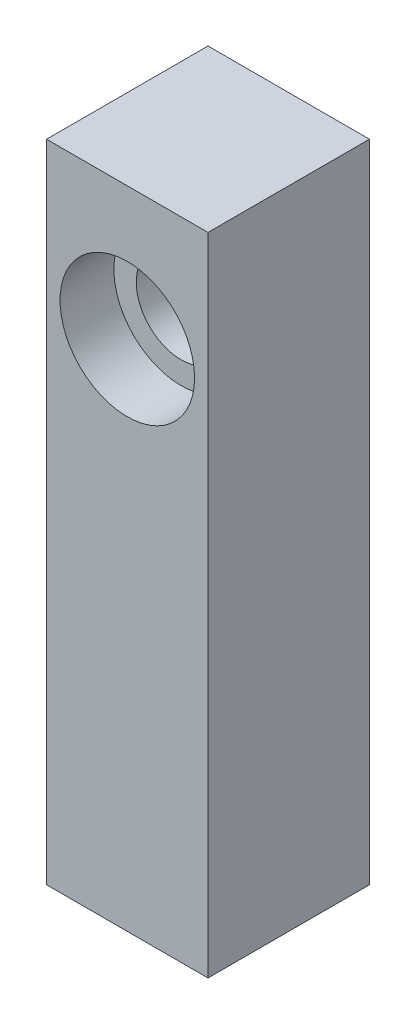
SolidWorks part; units mm, degrees
ref_plane "Front Plane" through (0, 0, 0) normal (0, 0, 1) x (1, 0, 0)
ref_plane "Top Plane" through (0, 0, 0) normal (0, 1, 0) x (1, 0, 0)
ref_plane "Right Plane" through (0, 0, 0) normal (1, 0, 0) x (0, 0, -1)
sketch "Sketch1" plane through (0, 0, 0) normal (0, 1, 0) x (1, 0, 0)
  line L1 (-42.9588, -4.732) -> (-24.9588, -4.732)
  line L2 (-42.9588, -4.732) -> (-42.9588, 13.268)
  line L3 (-42.9588, 13.268) -> (-24.9588, 13.268)
  line L4 (-24.9588, -4.732) -> (-24.9588, 13.268)
  dimension "D1" = 18
  dimension "D2" = 18
extrude "Boss-Extrude1" add sketch "Sketch1" along normal blind 72
sketch "Sketch2" plane through (0, 0, 4.732) normal (0, 0, 1) x (1, 0, 0)
  line L0 (-42.9588, 0) -> (-24.9588, 0) construction
  line L1 (-24.9588, 72) -> (-24.9588, 0) construction
  circle A0 centre (-33.9588, 57.2) radius 5
  dimension "D1" = 57.2
  dimension "D2" = 9
  dimension "D3" = 10
extrude "Cut-Extrude1" cut sketch "Sketch2" against normal through all
sketch "Sketch3" plane through (0, 0, 0) normal (0, -1, 0) x (1, 0, 0)
  line L0 (-24.9588, 4.732) -> (-24.9588, -13.268) construction
  line L1 (-24.9588, -13.268) -> (-42.9588, -13.268) construction
  circle A0 centre (-33.9588, -4.268) radius 3
  dimension "D1" = 6
  dimension "D2" = 9
  dimension "D3" = 9
hole_wizard "M6x1.0 Tapped Hole1" positions "Sketch4" profile "Sketch5" tap size "M6x1.0" standard "ANSI Metric"
sketch "Sketch4" plane through (0, 0, 0) normal (0, -1, 0) x (-1, 0, 0)
  point P0 (33.9588, 4.268)
sketch "Sketch5" plane through (-33.9588, 0, -4.268) normal (1, 0, 0) x (0, 0, -1)
  line L0 (0, 0) -> (0, 30.5022)
  line L1 (0, 30.5022) -> (2.5, 29)
  line L2 (2.5, 29) -> (2.5, 0)
  line L5 (2.5, 0) -> (0, 0)
  line L10 (0, 30.5022) -> (-2.5, 29) construction
  line L11 (0, -6.35) -> (0, 107.95) construction
  dimension "Tap Drill Dia." = 5
  dimension "Tap Drill Depth" = 29
  dimension "Drill Angle" = 118
cosmetic thread "Hole Thread1" parameters "D1"=26, "D2"=6
sketch "Sketch6" plane through (0, 0, 4.732) normal (0, 0, 1) x (1, 0, 0)
  circle A0 centre (-33.9588, 57.2) radius 7.5
  dimension "D1" = 15
extrude "Cut-Extrude2" cut sketch "Sketch6" against normal blind 6 contours A0
